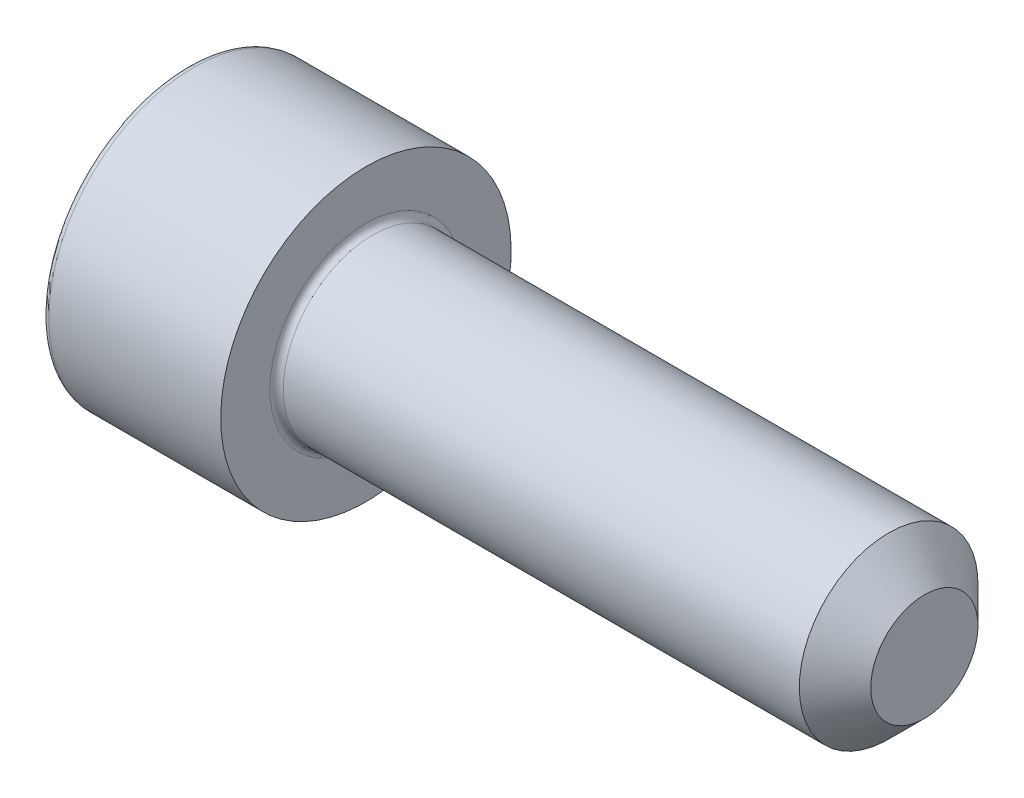
SolidWorks part; units mm, degrees
ref_plane "Спереди" through (0, 0, 0) normal (0, 0, 1) x (1, 0, 0)
ref_plane "Сверху" through (0, 0, 0) normal (0, 1, 0) x (1, 0, 0)
ref_plane "Справа" through (0, 0, 0) normal (1, 0, 0) x (0, 0, -1)
sketch "Эскиз1" plane through (0, 0, 0) normal (0, 0, 1) x (1, 0, 0)
  line L0 (0, 0) -> (0, 6.5)
  line L1 (0, 6.5) -> (8, 6.5)
  line L2 (8, 6.5) -> (8, 4)
  line L3 (8, 4) -> (33, 4)
  line L4 (33, 4) -> (33, 0)
  line L5 (33, 0) -> (0, 0) construction
  line L6 (0, 0) -> (33, 0)
  dimension "D1" = 13
  dimension "D2" = 8
  dimension "D3" = 8
  dimension "D4" = 25
revolve "Повернуть1" add sketch "Эскиз1" angle 360 about L5
cosmetic thread "Условное изображение резьбы1" parameters "D2"=6.619
sketch "Эскиз2" plane through (0, 0, 0) normal (-1, 0, 0) x (0, 0, 1)
  line L1 (-1.7321, 3) -> (-3.4641, 0)
  line L2 (-3.4641, 0) -> (-1.7321, -3)
  line L3 (-1.7321, -3) -> (1.7321, -3)
  line L4 (1.7321, -3) -> (3.4641, 0)
  line L5 (3.4641, 0) -> (1.7321, 3)
  line L6 (1.7321, 3) -> (-1.7321, 3)
  circle A0 centre (0, 0) radius 3 construction
  dimension "D1" = 6
extrude "Вырез-Вытянуть1" cut sketch "Эскиз2" against normal blind 2.5
fillet "Скругление1" radius 0.3 2 edges at (0, 6.5, 0) (8, 4, 0)
chamfer "Фаска1" distance 1.6 angle 45 1 edges at (33, 4, 0)
